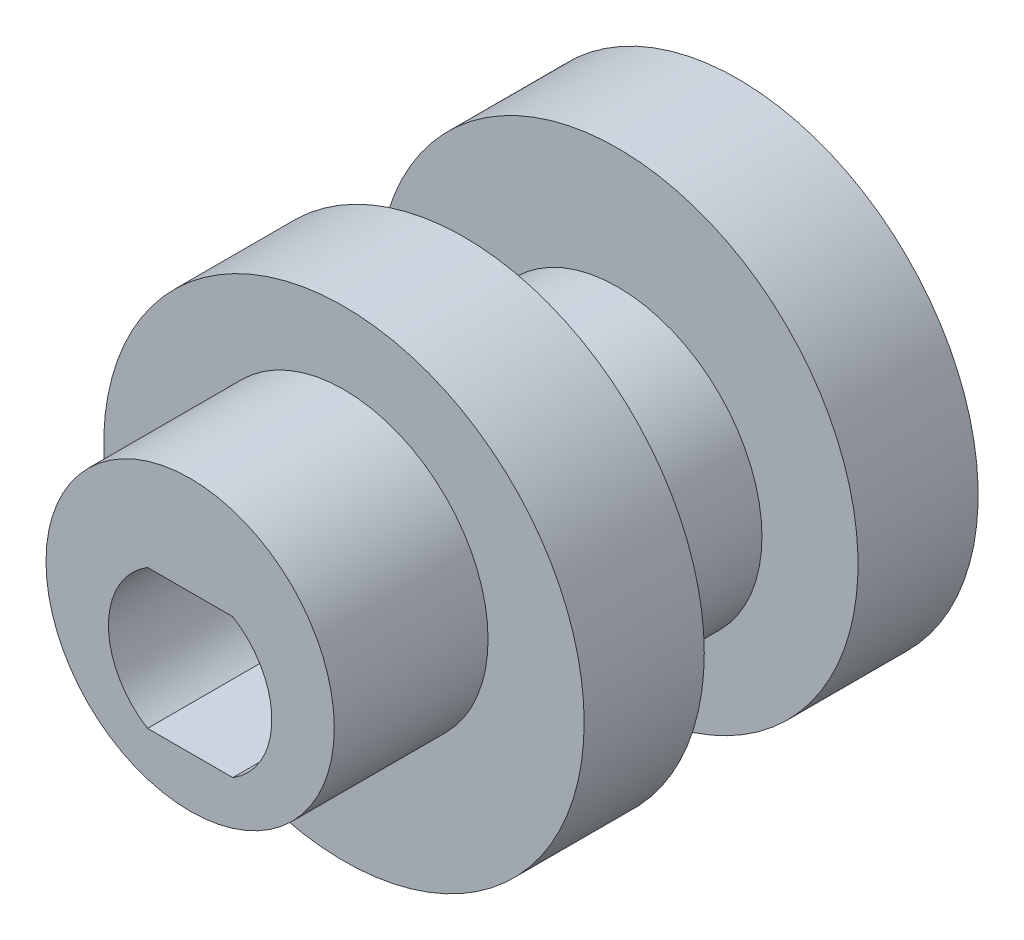
SolidWorks part; units mm, degrees
ref_plane "Front Plane" through (0, 0, 0) normal (0, 0, 1) x (1, 0, 0)
ref_plane "Top Plane" through (0, 0, 0) normal (0, 1, 0) x (1, 0, 0)
ref_plane "Right Plane" through (0, 0, 0) normal (1, 0, 0) x (0, 0, -1)
sketch "Sketch6" plane through (0, 0, 0) normal (0, 0, 1) x (1, 0, 0)
  circle A0 centre (0, 0) radius 10
  dimension "D1" = 20
extrude "Boss-Extrude4" add sketch "Sketch6" along normal mid plane 5
sketch "Sketch7" plane through (0, 0, 2.5) normal (0, 0, 1) x (1, 0, 0)
  circle A0 centre (0, 1) radius 6
  point P2 (0, 0)
  dimension "D1" = 12
  dimension "D2" = 1
extrude "Boss-Extrude5" add sketch "Sketch7" along normal blind 6.4
sketch "Sketch8" plane through (0, 0, -2.5) normal (0, 0, -1) x (-1, 0, 0)
  circle A0 centre (0, -1) radius 6
  point P2 (0, 0)
  dimension "D1" = 12
  dimension "D2" = 1
extrude "Boss-Extrude6" add sketch "Sketch8" along normal blind 6.4
sketch "Sketch12" plane through (0, 0, -8.9) normal (0, 0, -1) x (-1, 0, 0)
  circle A1 centre (0, 0) radius 10
  circle A2 centre (0, 0) radius 10
  dimension "D1" = 0
extrude "Boss-Extrude8" add sketch "Sketch12" along normal blind 5
sketch "Sketch11" plane through (0, 0, 2.5) normal (0, 0, 1) x (1, 0, 0)
  line L0 (-1.7748, -2.9) -> (1.7748, -2.9)
  line L1 (-1.6583, -2.5) -> (1.6583, -2.5) construction
  line L2 (-1.6583, -2.5) -> (-1.6583, 2.5) construction
  line L3 (-1.6583, 2.5) -> (1.6583, 2.5) construction
  line L4 (1.6583, -2.5) -> (1.6583, 2.5) construction
  line L5 (-1.6583, -2.5) -> (1.6583, 2.5) construction
  line L6 (-1.6583, 2.5) -> (1.6583, -2.5) construction
  line L7 (-1.7748, 2.9) -> (1.7748, 2.9)
  arc A0 (-1.6583, 2.5) -> (-1.6583, -2.5) centre (0, 0) ccw construction
  arc A1 (1.6583, -2.5) -> (1.6583, 2.5) centre (0, 0) ccw construction
  arc A2 (1.7748, -2.9) -> (1.7748, 2.9) centre (0, 0) ccw
  arc A3 (-1.7748, 2.9) -> (-1.7748, -2.9) centre (0, 0) ccw
  dimension "D1" = 6
  dimension "D2" = 2.5
  dimension "D3" = 0.4
extrude "Cut-Extrude1" cut sketch "Sketch11" against normal through all both and the other way through all
